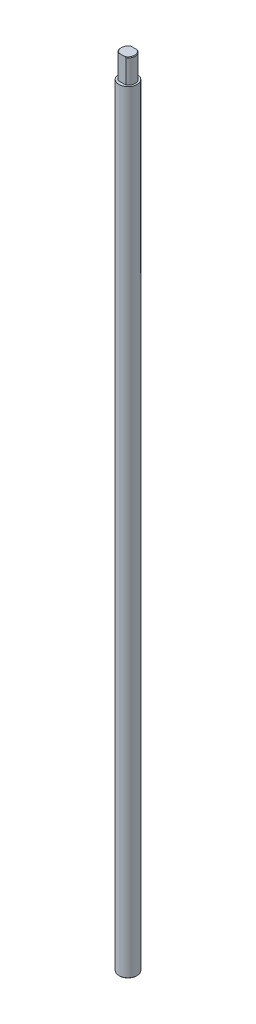
SolidWorks part; units mm, degrees
ref_plane "Front Plane" through (0, 0, 0) normal (0, 0, 1) x (1, 0, 0)
ref_plane "Top Plane" through (0, 0, 0) normal (0, 1, 0) x (1, 0, 0)
ref_plane "Right Plane" through (0, 0, 0) normal (1, 0, 0) x (0, 0, -1)
sketch "Sketch1" plane through (0, 0, 0) normal (0, 1, 0) x (1, 0, 0)
  circle A0 centre (0, 0) radius 7.5
  dimension "D1" = 15
extrude "Boss-Extrude1" add sketch "Sketch1" along normal blind 640 contours A0
sketch "Sketch2" plane through (0, 640, 0) normal (0, 1, 0) x (1, 0, 0)
  circle A0 centre (0, 0) radius 6
  dimension "D1" = 12
extrude "Boss-Extrude2" add sketch "Sketch2" along normal blind 20
chamfer "Chamfer1" distance 0.5 angle 45 1 edges at (0, 660, 6)
chamfer "Chamfer2" distance 0.5 angle 45 1 edges at (0, 0, 7.5)
sketch "Sketch3" plane through (0, 0, 0) normal (1, 0, 0) x (0, 0, -1)
  line L0 (5.5, 660) -> (-5.5, 660) construction
  line L1 (5.5, 660) -> (-5.5, 660)
  line L2 (0, 638.8414) -> (0, 668.3013) construction
  line L3 (11.7201, 640) -> (5, 640)
  line L4 (6, 640) -> (-6, 640) construction
  line L5 (5, 640) -> (5, 665.5182)
  line L6 (5, 665.5182) -> (13.8923, 665.5182)
  line L7 (13.8923, 665.5182) -> (13.8923, 640)
  line L8 (13.8923, 640) -> (11.7201, 640)
  line L9 (-13.8923, 640) -> (-11.7201, 640)
  line L10 (-11.7201, 640) -> (-5, 640)
  line L11 (-13.8923, 665.5182) -> (-13.8923, 640)
  line L12 (-5, 665.5182) -> (-13.8923, 665.5182)
  line L13 (-5, 640) -> (-5, 665.5182)
  dimension "D1" = 5
extrude "Cut-Extrude1" cut sketch "Sketch3" against normal through all both and the other way through all
